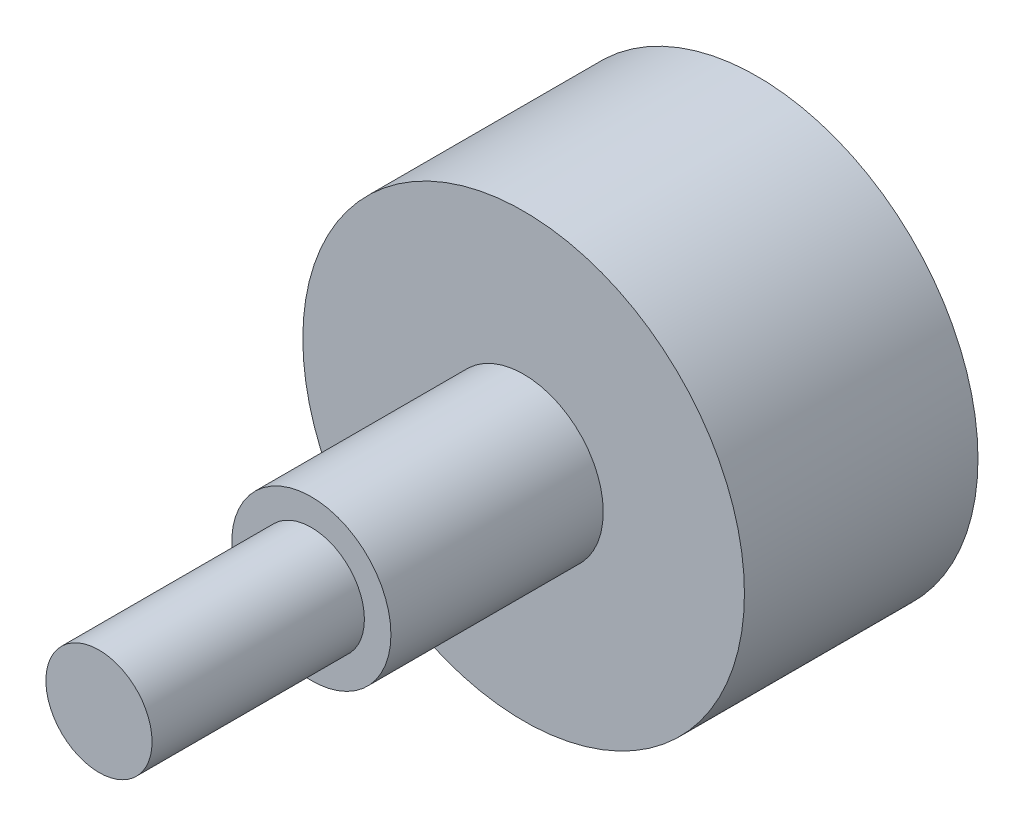
SolidWorks part; units mm, degrees
ref_plane "Front" through (0, 0, 0) normal (0, 0, 1) x (1, 0, 0)
ref_plane "Top" through (0, 0, 0) normal (0, 1, 0) x (1, 0, 0)
ref_plane "Right" through (0, 0, 0) normal (1, 0, 0) x (0, 0, -1)
sketch "Sketch1" plane through (0, 0, 0) normal (0, 0, 1) x (1, 0, 0)
  circle A0 centre (0, 0) radius 13.208
  dimension "D1" = 26.416
extrude "Extrude1" add sketch "Sketch1" along normal blind 13.97
sketch "Sketch2" plane through (0, 0, 13.97) normal (0, 0, 1) x (1, 0, 0)
  circle A0 centre (0, 0) radius 4.7625
  dimension "D1" = 9.525
extrude "Extrude2" add sketch "Sketch2" along normal blind 12.7
sketch "Sketch3" plane through (0, 0, 26.67) normal (0, 0, 1) x (1, 0, 0)
  circle A0 centre (0, 0) radius 3.175
  dimension "D1" = 6.35
extrude "Extrude3" add sketch "Sketch3" along normal blind 12.7
